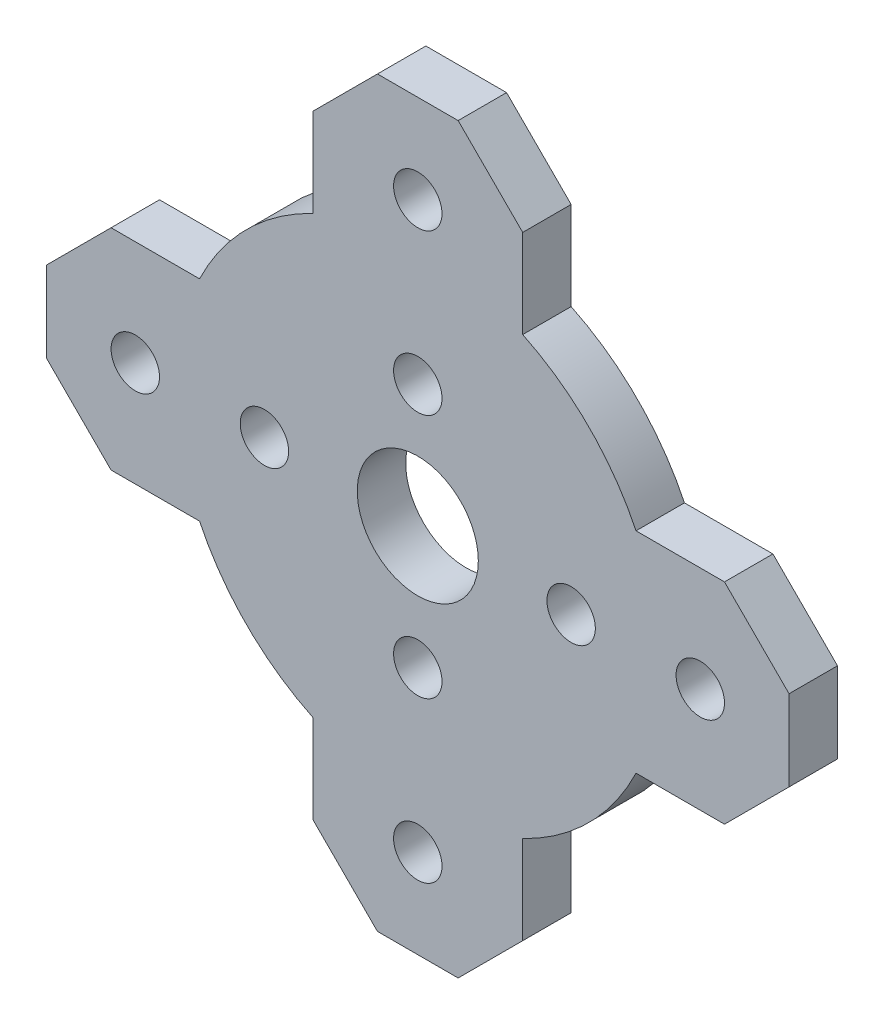
SolidWorks part; units mm, degrees
ref_plane "Front Plane" through (0, 0, 0) normal (0, 0, 1) x (1, 0, 0)
ref_plane "Top Plane" through (0, 0, 0) normal (0, 1, 0) x (1, 0, 0)
ref_plane "Right Plane" through (0, 0, 0) normal (1, 0, 0) x (0, 0, -1)
sketch "Sketch1" plane through (0, 0, 0) normal (0, 0, 1) x (1, 0, 0)
  line L0 (-6.5, 23) -> (6.5, 23)
  line L5 (-6.5, -23) -> (6.5, -23) construction
  line L6 (-6.5, -23) -> (-6.5, 23) construction
  line L7 (-9.5, 7.6) -> (9.5, 7.6) construction
  line L8 (-9.5, 7.6) -> (-9.5, -7.6) construction
  line L9 (-9.5, -7.6) -> (9.5, -7.6) construction
  line L10 (9.5, 7.6) -> (9.5, -7.6) construction
  line L11 (-9.5, 7.6) -> (9.5, -7.6) construction
  line L12 (-9.5, -7.6) -> (9.5, 7.6) construction
  line L13 (-6.5, 23) -> (6.5, 23) construction
  line L14 (6.5, -23) -> (6.5, 23) construction
  line L15 (-6.5, -23) -> (2.1478, 7.6) construction
  line L16 (-4.0794, 14.4346) -> (6.5, -23) construction
  line L17 (-23, -6.5) -> (23, -6.5) construction
  line L18 (-23, -6.5) -> (-23, 6.5) construction
  line L19 (-23, 6.5) -> (23, 6.5) construction
  line L20 (23, -6.5) -> (23, 6.5) construction
  line L21 (-23, -6.5) -> (23, 6.5) construction
  line L22 (-23, 6.5) -> (23, -6.5) construction
  line L23 (6.5, 23) -> (6.5, 13.5185)
  line L24 (-6.5, 23) -> (-6.5, 13.5185)
  line L25 (-23, 6.5) -> (-13.5185, 6.5)
  line L26 (-23, 6.5) -> (-23, -6.5)
  line L27 (-23, -6.5) -> (-13.5185, -6.5)
  line L28 (23, 6.5) -> (13.5185, 6.5)
  line L29 (23, 6.5) -> (23, -6.5)
  line L30 (23, -6.5) -> (13.5185, -6.5)
  line L31 (-6.5, -23) -> (6.5, -23)
  line L32 (6.5, -23) -> (6.5, -13.5185)
  line L33 (-6.5, -23) -> (-6.5, -13.5185)
  line L34 (-6.5, 23) -> (-4.0794, 14.4346) construction
  line L35 (2.1478, 7.6) -> (4.0794, 14.4346) construction
  line L36 (4.0794, 14.4346) -> (6.5, 23) construction
  line L37 (-23, 0) -> (23, 0) construction
  line L38 (0, 23) -> (0, -23) construction
  circle A0 centre (0, 7.6) radius 1.5
  circle A1 centre (9.5, 0) radius 1.5
  circle A2 centre (-9.5, 0) radius 1.5
  circle A3 centre (0, -7.6) radius 1.5
  arc A4 (-13.5185, -6.5) -> (-6.5, -13.5185) centre (0, 0) ccw
  arc A5 (-14.4346, 4.0794) -> (-14.4346, -4.0794) centre (0, 0) ccw construction
  arc A6 (-4.0794, -14.4346) -> (4.0794, -14.4346) centre (0, 0) ccw construction
  arc A7 (6.5, -13.5185) -> (13.5185, -6.5) centre (0, 0) ccw
  arc A8 (-6.5, -13.5185) -> (-4.0794, -14.4346) centre (0, 0) ccw construction
  arc A9 (4.0794, -14.4346) -> (6.5, -13.5185) centre (0, 0) ccw construction
  arc A10 (13.5185, -6.5) -> (14.4346, -4.0794) centre (0, 0) ccw construction
  arc A11 (13.5185, 6.5) -> (6.5, 13.5185) centre (0, 0) ccw
  arc A12 (14.4346, -4.0794) -> (14.4346, 4.0794) centre (0, 0) ccw construction
  arc A13 (14.4346, 4.0794) -> (13.5185, 6.5) centre (0, 0) ccw construction
  arc A14 (-4.0794, 14.4346) -> (-6.5, 13.5185) centre (0, 0) ccw construction
  arc A15 (-6.5, 13.5185) -> (-13.5185, 6.5) centre (0, 0) ccw
  arc A16 (4.0794, 14.4346) -> (-4.0794, 14.4346) centre (0, 0) ccw construction
  arc A17 (6.5, 13.5185) -> (4.0794, 14.4346) centre (0, 0) ccw construction
  arc A18 (-13.5185, 6.5) -> (-14.4346, 4.0794) centre (0, 0) ccw construction
  arc A19 (-14.4346, -4.0794) -> (-13.5185, -6.5) centre (0, 0) ccw construction
  circle A20 centre (0, 17.5) radius 1.5
  circle A21 centre (17.5, 0) radius 1.5
  circle A22 centre (0, -17.5) radius 1.5
  circle A23 centre (-17.5, 0) radius 1.5
  circle A24 centre (0, 0) radius 3.75
  point P0 (0, 0)
  point P5 (0, 0)
  dimension "D1" = 3
  dimension "D4" = 30
  dimension "D8" = 3
  dimension "D13" = 7.5
  dimension "D2" = 15.2
  dimension "D3" = 19
  dimension "D5" = 13
  dimension "D6" = 46
  dimension "D7" = 46
  dimension "D9" = 17.5
  dimension "D10" = 17.5
  dimension "D11" = 17.5
  dimension "D12" = 17.5
extrude "Boss-Extrude1" add sketch "Sketch1" along normal blind 3
chamfer "Chamfer1" distance 4 angle 45 8 edges at (-23, 6.5, 1.5) (-23, -6.5, 1.5) (-6.5, -23, 1.5) (6.5, -23, 1.5) (23, -6.5, 1.5) (23, 6.5, 1.5) (6.5, 23, 1.5) (-6.5, 23, 1.5)
equation "\"D10@Sketch1\"=\"D9@Sketch1\""
equation "\"D11@Sketch1\"=\"D9@Sketch1\""
equation "\"D12@Sketch1\"=\"D9@Sketch1\""
equation "\"D6@Sketch1\"=\"D7@Sketch1\""
